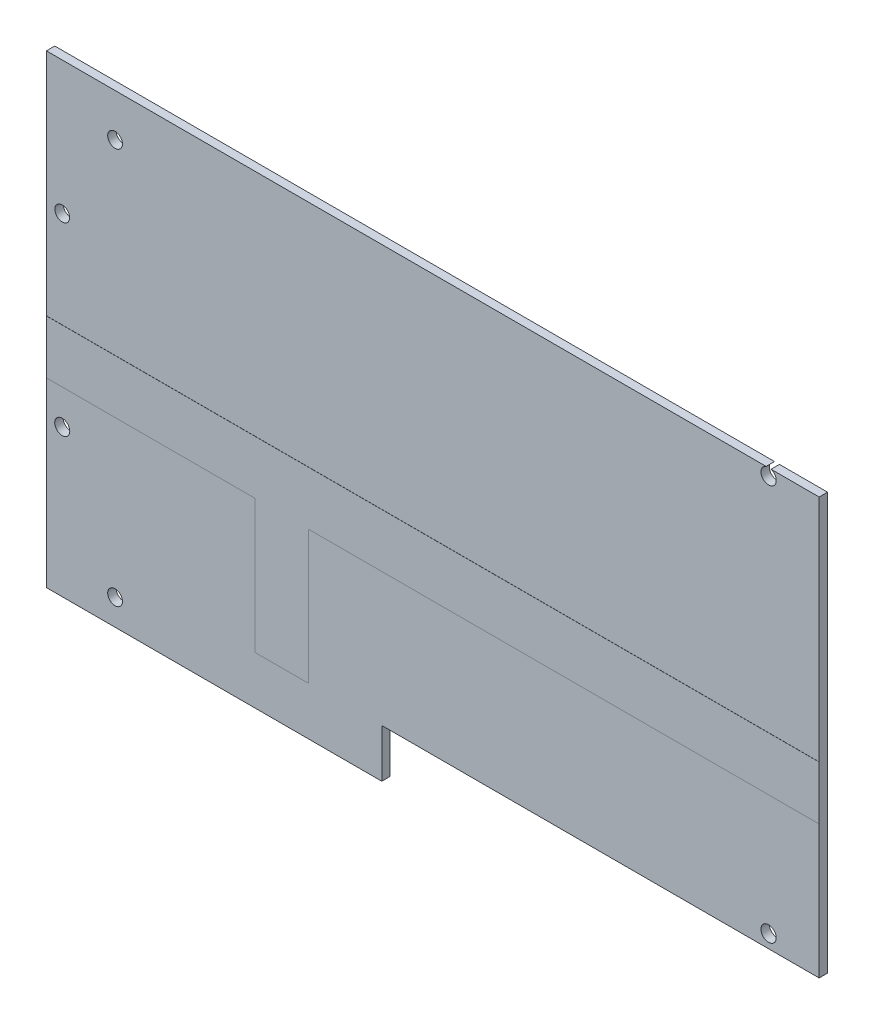
SolidWorks part; units mm, degrees
ref_plane "Front Plane" through (0, 0, 0) normal (0, 0, 1) x (1, 0, 0)
ref_plane "Top Plane" through (0, 0, 0) normal (0, 1, 0) x (1, 0, 0)
ref_plane "Right Plane" through (0, 0, 0) normal (1, 0, 0) x (0, 0, -1)
sketch "Sketch1" plane through (0, 0, 0) normal (0, 0, 1) x (1, 0, 0)
  line L1 (-73.152, 48.514) -> (73.152, 48.514)
  line L2 (-73.152, 48.514) -> (-73.152, -30.353)
  line L3 (-73.152, -30.353) -> (73.152, -30.353)
  line L4 (73.152, 48.514) -> (73.152, -30.353)
  dimension "D1" = 146.304
  dimension "D2" = 78.867
  dimension "D4" = 73.152
  dimension "D3" = 48.514
extrude "Boss-Extrude1" add sketch "Sketch1" along normal blind 1.5875
sketch "Sketch3" plane through (0, 0, 1.5875) normal (0, 0, 1) x (1, 0, 0)
  line L0 (-73.152, 0) -> (73.152, 0)
  line L1 (-73.152, 48.514) -> (-73.152, -30.353) construction
  line L2 (73.152, -30.353) -> (73.152, 48.514) construction
  dimension "D1" = 0
sketch "Sketch4" plane through (0, 0, 1.5875) normal (0, 0, 1) x (1, 0, 0)
  line L0 (-73.152, 48.514) -> (-73.152, -30.353) construction
  line L1 (-73.152, 5.08) -> (73.152, 5.08)
  line L2 (-73.152, 5.08) -> (-73.152, -5.08)
  line L4 (73.152, 5.08) -> (73.152, -5.08)
  line L5 (73.152, -30.353) -> (73.152, 48.514) construction
  line L7 (-73.152, -30.353) -> (73.152, -30.353) construction
  line L9 (-33.6423, -5.08) -> (-33.6423, -30.353)
  line L10 (-33.6423, -30.353) -> (-23.4823, -30.353)
  line L11 (-23.4823, -5.08) -> (-23.4823, -30.353)
  line L13 (-73.152, -5.08) -> (-33.6423, -5.08)
  line L14 (-23.4823, -5.08) -> (73.152, -5.08)
  line L15 (-73.152, 0) -> (73.152, 0) construction
  dimension "D3" = 10.16
  dimension "D1" = 10.16
  dimension "D2" = 5.08
  dimension "D4" = 10.16
  dimension "D5" = 39.5097
extrude "Boss-Extrude2" add sketch "Sketch4" along normal blind 0.0254 and the other way blind 1.6254
sketch "Sketch5" plane through (0, 0, 1.5875) normal (0, 0, 1) x (1, 0, 0)
  line L0 (-23.4823, -30.353) -> (73.152, -30.353) construction
  circle A1 centre (63.58, 47.147) radius 1.445
  circle A3 centre (63.58, -27.853) radius 1.445
  dimension "D4" = 2.89
  dimension "D3" = 2.89
  dimension "D1" = 75
  dimension "D2" = 2.5
extrude "Cut-Extrude1" cut sketch "Sketch5" against normal through all
mirror "Mirror1" [suppressed] about plane through (0, 0, 0) normal (1, 0, 0)
mirror "Mirror2" [suppressed] about plane through (0, 0, 0) normal (0, 1, 0)
mirror "Mirror3" [suppressed] about plane through (0, 0, 0) normal (1, 0, 0)
sketch "Sketch7" plane through (0, 0, 1.5875) normal (0, 0, 1) x (1, 0, 0)
  line L0 (-73.152, -30.353) -> (-33.6423, -30.353) construction
  line L1 (-73.152, -30.353) -> (-9.652, -30.353)
  line L2 (-73.152, -30.353) -> (-73.152, -39.497)
  line L3 (-73.152, -39.497) -> (-9.652, -39.497)
  line L4 (-9.652, -30.353) -> (-9.652, -39.497)
  dimension "D1" = 9.144
  dimension "D2" = 63.5
extrude "Boss-Extrude3" add sketch "Sketch7" against normal up to surface (1.5875 mm away) up to face at (-53.3972, -17.7165, 0)
sketch "Sketch6" plane through (0, 0, 1.5875) normal (0, 0, 1) x (1, 0, 0)
  line L0 (-73.152, 0) -> (73.152, 0) construction
  line L1 (-73.152, 48.514) -> (-73.152, 5.08) construction
  line L2 (-73.152, -5.08) -> (-73.152, -39.497) construction
  circle A0 centre (-70.152, 23.35) radius 1.397
  circle A1 centre (-70.152, -11.65) radius 1.425
  circle A2 centre (-60.152, 40.425) radius 1.397
  circle A3 centre (-60.152, -34.575) radius 1.397
  dimension "D1" = 2.794
  dimension "D10" = 2.794
  dimension "D11" = 2.794
  dimension "D2" = 23.35
  dimension "D3" = 3
  dimension "D4" = 11.65
  dimension "D5" = 3
  dimension "D6" = 10
  dimension "D7" = 10
  dimension "D8" = 17.075
  dimension "D9" = 22.925
extrude "Cut-Extrude2" cut sketch "Sketch6" against normal through all
equation "\"D4@Sketch1\"=\"D1@Sketch1\"/2"
equation "\"D3@Sketch4\"=\"D1@Sketch4\""
equation "\"D2@Sketch4\"=\"D1@Sketch4\"/2"
equation "\"D4@Sketch4\"=\"D1@Sketch4\""
equation "\"D3@Sketch5\"=\"D4@Sketch5\""
equation "\"D5@Sketch6\"=\"D3@Sketch6\""
equation "\"D10@Sketch6\"=\"D1@Sketch6\""
equation "\"D11@Sketch6\"=\"D10@Sketch6\""
